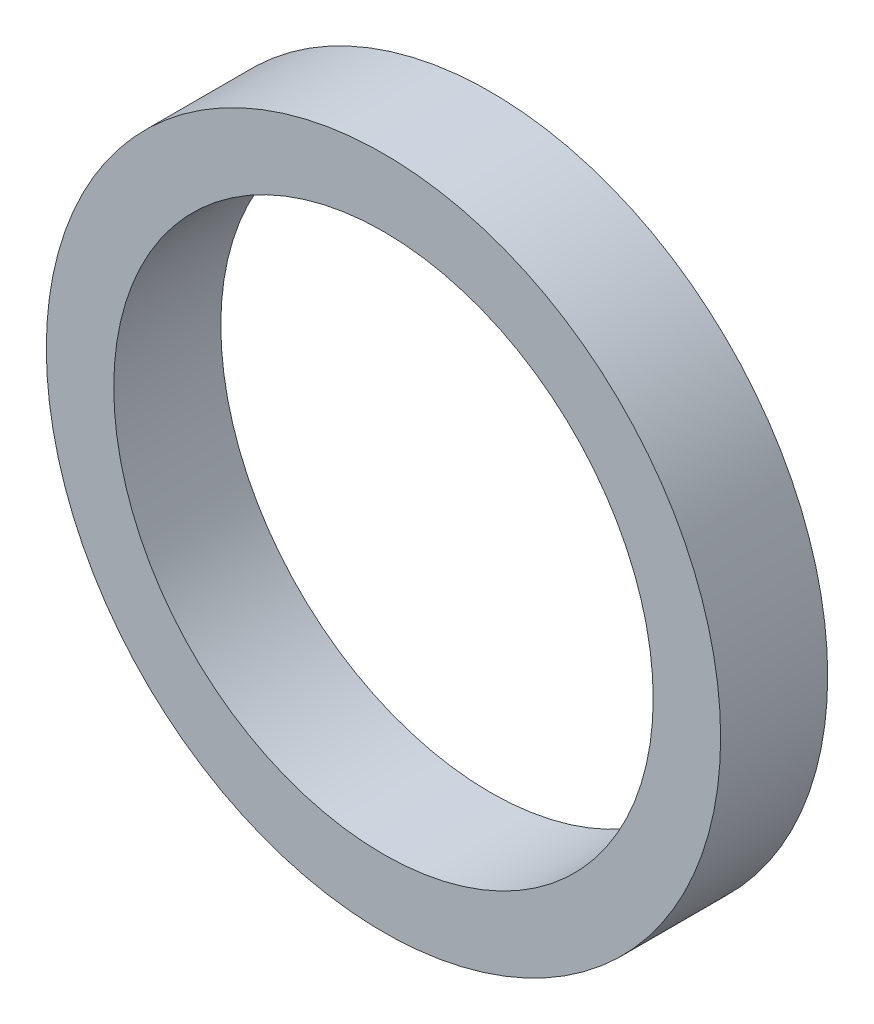
SolidWorks part; units mm, degrees
ref_plane "Front Plane" through (0, 0, 0) normal (0, 0, 1) x (1, 0, 0)
ref_plane "Top Plane" through (0, 0, 0) normal (0, 1, 0) x (1, 0, 0)
ref_plane "Right Plane" through (0, 0, 0) normal (1, 0, 0) x (0, 0, -1)
sketch "Sketch1" plane through (0, 0, 0) normal (0, 0, 1) x (1, 0, 0)
  circle A0 centre (0, 0) radius 4
  circle A1 centre (0, 0) radius 5
  dimension "D1" = 8
  dimension "D2" = 1
extrude "Boss-Extrude1" add sketch "Sketch1" along normal blind 1.5875
